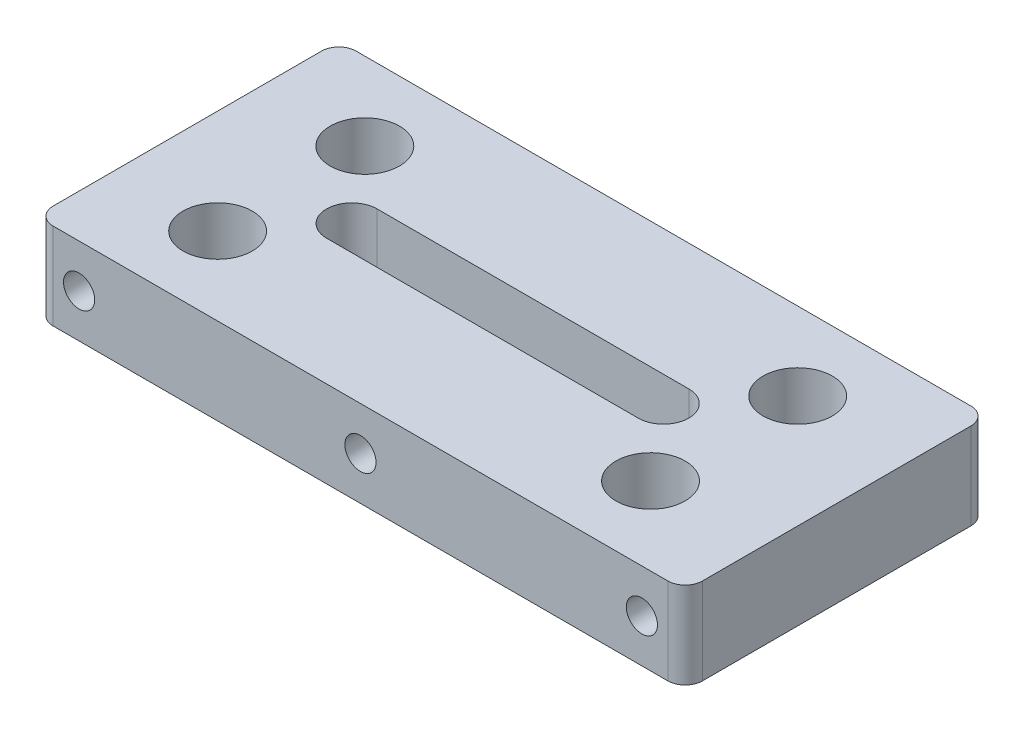
SolidWorks part; units mm, degrees
ref_plane "Front Plane" through (0, 0, 0) normal (0, 0, 1) x (1, 0, 0)
ref_plane "Top Plane" through (0, 0, 0) normal (0, 1, 0) x (1, 0, 0)
ref_plane "Right Plane" through (0, 0, 0) normal (1, 0, 0) x (0, 0, -1)
sketch "Sketch1" plane through (0, 0, 0) normal (0, 1, 0) x (1, 0, 0)
  line L1 (0, 0) -> (75, 0)
  line L2 (0, 0) -> (0, 35)
  line L3 (0, 35) -> (75, 35)
  line L4 (75, 0) -> (75, 35)
  dimension "D1" = 35
  dimension "D2" = 75
extrude "Boss-Extrude1" add sketch "Sketch1" along normal blind 10
sketch "Sketch2" plane through (0, 0, 0) normal (0, 0, 1) x (1, 0, 0)
  circle A0 centre (5, 5) radius 1.8
  circle A1 centre (37.5, 5) radius 1.8
  circle A2 centre (70, 5) radius 1.8
  point P6 (5, 5)
  point P7 (70, 5)
  dimension "D1" = 3
extrude "Cut-Extrude1" cut sketch "Sketch2" against normal blind 10
sketch "Sketch3" plane through (0, 0, -35) normal (0, 0, -1) x (-1, 0, 0)
  line L0 (-75, 5) -> (0, 5) construction
  line L1 (-75, 10) -> (-75, 0) construction
  line L2 (0, 10) -> (0, 0) construction
  circle A0 centre (-5, 5) radius 1.8
  circle A1 centre (-37.5, 5) radius 1.8
  circle A2 centre (-70, 5) radius 1.8
  point P6 (-5, 5)
  point P7 (-70, 5)
extrude "Cut-Extrude2" cut sketch "Sketch3" against normal blind 10
sketch "Sketch4" plane through (0, 0, 0) normal (0, -1, 0) x (1, 0, 0)
  line L15 (19, -17.5) -> (55, -17.5) construction
  line L16 (19, -14.5767) -> (55, -14.5767)
  line L17 (19, -20.4233) -> (55, -20.4233)
  circle A0 centre (12, -9) radius 4
  circle A1 centre (62, -9) radius 4
  circle A2 centre (62, -26) radius 4
  circle A3 centre (12, -26) radius 4
  arc A6 (19, -14.5767) -> (19, -20.4233) centre (19, -17.5) ccw
  arc A7 (55, -20.4233) -> (55, -14.5767) centre (55, -17.5) ccw
  point P24 (37, -17.5)
  dimension "D2" = 2
extrude "Cut-Extrude4" cut sketch "Sketch4" against normal through all
fillet "Fillet1" radius 2 4 edges at (0, 5, -35) (0, 5, 0) (75, 5, 0) (75, 5, -35)
